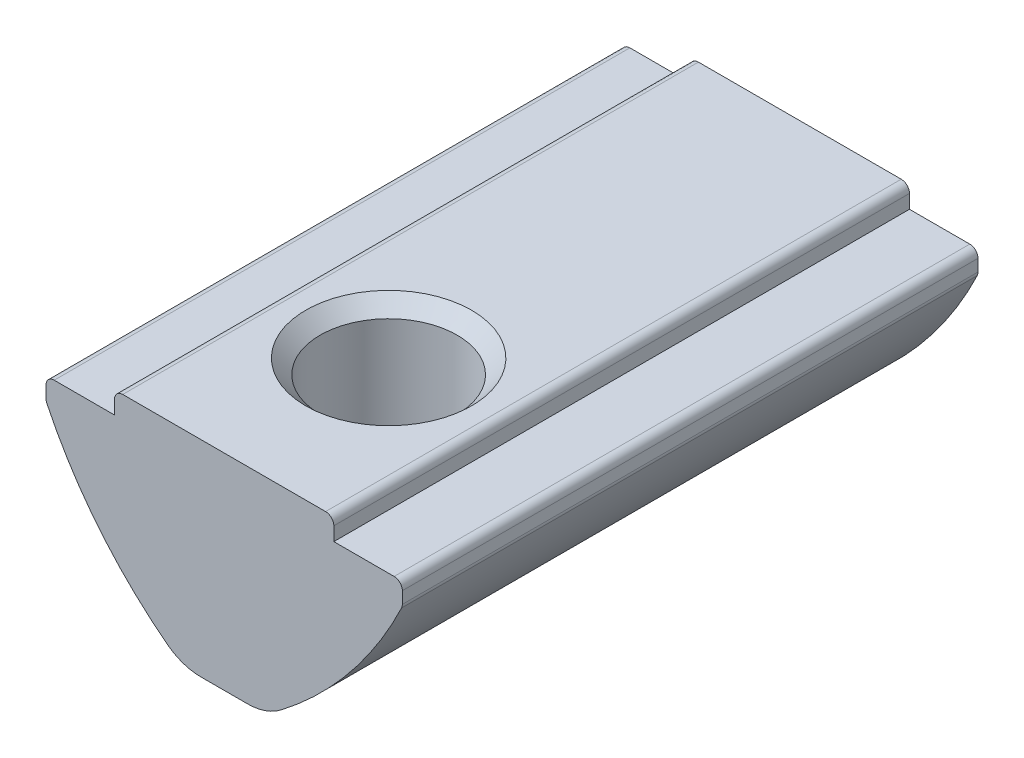
SolidWorks part; units mm, degrees
ref_plane "Спереди" through (0, 0, 0) normal (0, 0, 1) x (1, 0, 0)
ref_plane "Сверху" through (0, 0, 0) normal (0, 1, 0) x (1, 0, 0)
ref_plane "Справа" through (0, 0, 0) normal (1, 0, 0) x (0, 0, -1)
sketch "Эскиз1" plane through (0, 0, 0) normal (0, 0, 1) x (1, 0, 0)
  line L0 (-4, 0) -> (4, 0)
  line L5 (-4, 0) -> (-4, -0.8)
  line L6 (-4, -0.8) -> (-6.5, -0.8)
  line L7 (-6.5, -0.8) -> (-6.5, -1.6)
  line L8 (4, 0) -> (4, -0.8)
  line L9 (4, -0.8) -> (6.5, -0.8)
  line L10 (6.5, -0.8) -> (6.5, -1.6)
  line L11 (-1.5, -7.5) -> (1.5, -7.5)
  arc A0 (-6.5, -1.6) -> (-1.5, -7.5) centre (7.0567, 4.82) ccw
  arc A1 (1.5, -7.5) -> (6.5, -1.6) centre (-7.0567, 4.82) ccw
  point P0 (0, -7.5)
  point P4 (0, 0)
  dimension "D7" = 15
  dimension "D1" = 8
  dimension "D2" = 13
  dimension "D3" = 0.8
  dimension "D4" = 3
  dimension "D5" = 0.8
  dimension "D6" = 7.5
extrude "Бобышка-Вытянуть1" add sketch "Эскиз1" along normal mid plane 21
fillet "Скругление1" radius 0.3 6 edges at (6.5, -1.6, 0) (6.5, -0.8, 0) (-6.5, -0.8, 0) (-6.5, -1.6, 0) (4, 0, 0) (-4, 0, 0)
fillet "Скругление2" radius 2 2 edges at (1.5, -7.5, 0) (-1.5, -7.5, 0)
hole_wizard "Отверстие обработанное метчиком M62" positions "Эскиз2" profile "Эскиз4" tap size "M6" standard "ISO" end condition through all
sketch "Эскиз2" plane through (0, 0, 0) normal (0, 1, 0) x (1, 0, 0)
  line L0 (3.7, -10.5) -> (-3.7, -10.5) construction
  point P0 (0, -4.5)
  dimension "D1" = 6
sketch "Эскиз4" plane through (0, 0, 4.5) normal (1, 0, 0) x (0, 0, 1)
  line L0 (0, 0) -> (0, 7.5)
  line L1 (0, 7.5) -> (2.5, 7.5)
  line L2 (2.5, 7.5) -> (2.5, 0.525)
  line L3 (2.5, 0.525) -> (3.025, 0)
  line L5 (3.025, 0) -> (0, 0)
  line L6 (-2.5, 0.525) -> (-3.025, 0) construction
  line L11 (0, -6.35) -> (0, 107.95) construction
  dimension "Диаметр проходного сверла" = 5
  dimension "Глубина проходного сверла" = 7.5
  dimension "Диаметр передней зенковки" = 6.05
  dimension "Угол передней зенковки" = 90
cosmetic thread "Отверстие резьбы1" parameters "D2"=6
sketch "Эскиз5" plane through (0, 0, 0) normal (1, 0, 0) x (0, 0, -1)
  line L1 (6.5, -4.3) -> (6.5, -8.3) construction
  line L2 (10.5, -7.0877) -> (10.5, -1.6618) construction
  line L3 (6.5, -4.3) -> (6.5, -8.3)
  line L5 (10.5, -7.5) -> (-2.1485, -7.5) construction
  arc A0 (6.5, -4.3) -> (6.5, -8.3) centre (6.5, -6.3) ccw
  point P3 (4, -7.4722)
  dimension "D3" = 2
  dimension "D1" = 0.8
  dimension "D2" = 4
revolve "Повернуть1" add sketch "Эскиз5" angle 360 about L1
